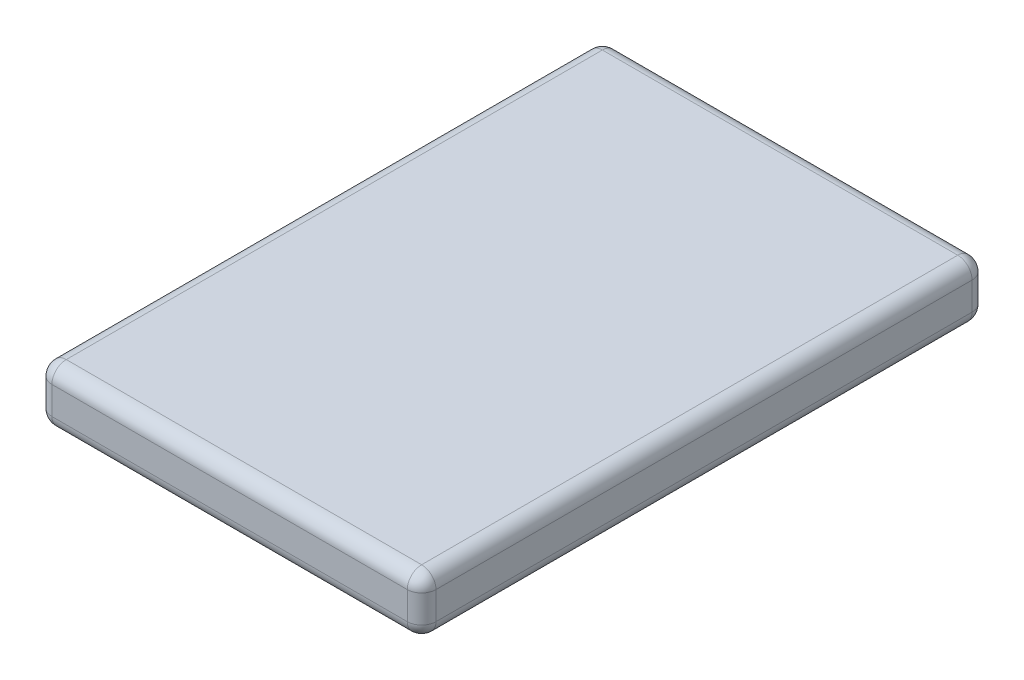
SolidWorks part; units mm, degrees
ref_plane "Front Plane" through (0, 0, 0) normal (0, 0, 1) x (1, 0, 0)
ref_plane "Top Plane" through (0, 0, 0) normal (0, 1, 0) x (1, 0, 0)
ref_plane "Right Plane" through (0, 0, 0) normal (1, 0, 0) x (0, 0, -1)
sketch "Sketch2" plane through (0, 0, 0) normal (0, 0, 1) x (1, 0, 0)
  line L1 (-15.73, -2.5) -> (15.73, -2.5)
  line L2 (-17, -1.23) -> (-17, 1.23)
  line L3 (-15.73, 2.5) -> (15.73, 2.5)
  line L4 (17, -1.23) -> (17, 1.23)
  line L5 (-17, -2.5) -> (17, 2.5) construction
  line L6 (-17, 2.5) -> (17, -2.5) construction
  arc A0 (-15.73, -2.5) -> (-17, -1.23) centre (-15.73, -1.23) cw
  arc A1 (17, 1.23) -> (15.73, 2.5) centre (15.73, 1.23) ccw
  arc A2 (17, -1.23) -> (15.73, -2.5) centre (15.73, -1.23) cw
  arc A3 (-15.73, 2.5) -> (-17, 1.23) centre (-15.73, 1.23) ccw
  point P0 (0, 0)
  dimension "D3" = 1.27
  dimension "D1" = 34
  dimension "D2" = 5
extrude "Boss-Extrude1" add sketch "Sketch2" along normal blind 50
fillet "Fillet1" radius 1.27 16 edges at (0, -2.5, 50) (-16.628, -2.128, 50) (-17, 0, 50) (-16.628, 2.128, 50) (0, 2.5, 50) (16.628, 2.128, 50) (17, 0, 50) (16.628, -2.128, 0) (0, -2.5, 0) (-16.628, -2.128, 0) (-17, 0, 0) (-16.628, 2.128, 0) (0, 2.5, 0) (16.628, 2.128, 0) (16.628, -2.128, 50) (17, 0, 0)
equation "\"D1@Boss-Extrude1\"=50mm"
